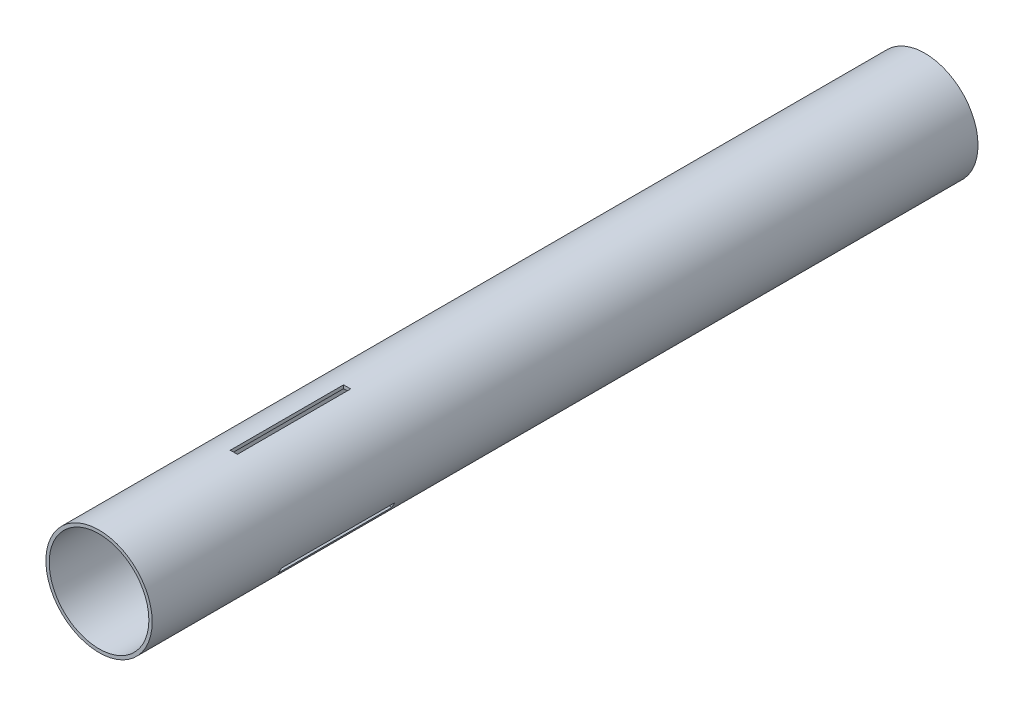
SolidWorks part; units mm, degrees
ref_plane "Front Plane" through (0, 0, 0) normal (0, 0, 1) x (1, 0, 0)
ref_plane "Top Plane" through (0, 0, 0) normal (0, 1, 0) x (1, 0, 0)
ref_plane "Right Plane" through (0, 0, 0) normal (1, 0, 0) x (0, 0, -1)
sketch "Sketch1" plane through (0, 0, 0) normal (0, 0, 1) x (1, 0, 0)
  circle A0 centre (0, 0) radius 23.6982
  circle A1 centre (0, 0) radius 22.225
  dimension "D1" = 47.3964
  dimension "D2" = 44.45
extrude "Boss-Extrude1" add sketch "Sketch1" along normal blind 368.3
ref_plane "Plane1" through (0, 100, 0) normal (0, 1, 0) x (1, 0, 0)
sketch "Sketch2" plane through (0, 100, 0) normal (0, 1, 0) x (1, 0, 0)
  line L0 (-23.6982, -368.3) -> (23.6982, -368.3) construction
  line L3 (1.5875, -308.229) -> (1.5875, -257.683)
  line L4 (-1.5875, -308.229) -> (-1.5875, -257.683)
  line L5 (-1.5875, -257.683) -> (1.5875, -257.683)
  line L6 (-1.5875, -308.229) -> (1.5875, -308.229)
  dimension "D1" = 60.071
  dimension "D2" = 50.546
  dimension "D3" = 3.175
extrude "Cut-Extrude1" cut sketch "Sketch2" against normal up to next
pattern_circular "CirPattern2" count 3 over 360 about axis through (0, 0, 0) along (0, 0, 1) of "Cut-Extrude1"
